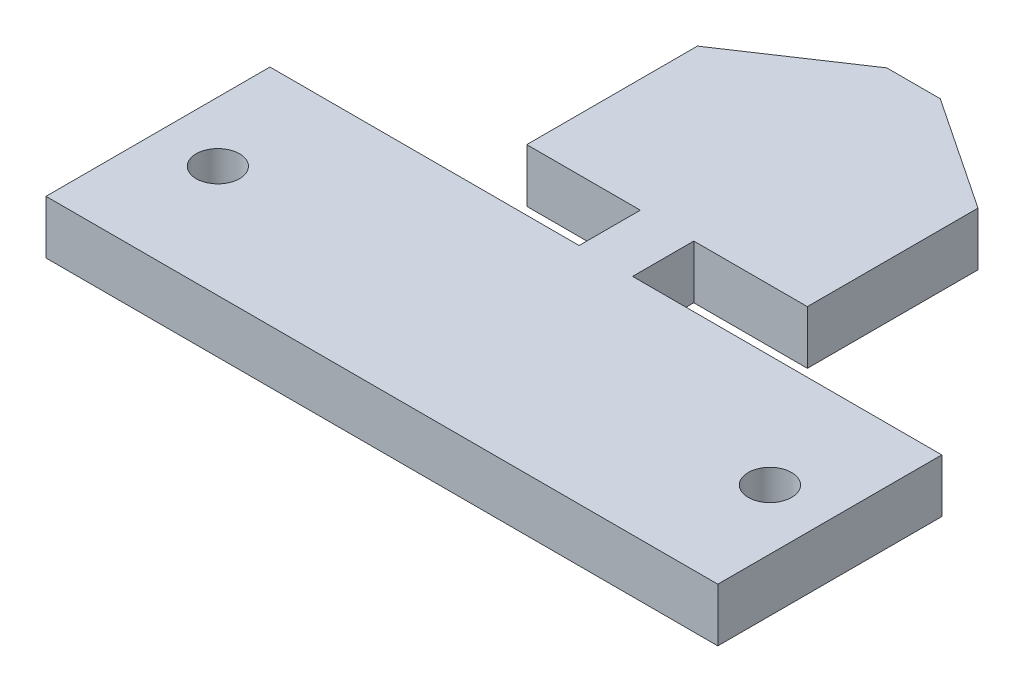
SolidWorks part; units mm, degrees
ref_plane "Front" through (0, 0, 0) normal (0, 0, 1) x (1, 0, 0)
ref_plane "Top" through (0, 0, 0) normal (0, 1, 0) x (1, 0, 0)
ref_plane "Right" through (0, 0, 0) normal (1, 0, 0) x (0, 0, -1)
sketch "Sketch1" plane through (0, 0, 0) normal (0, 1, 0) x (1, 0, 0)
  line L0 (-1.7907, 2.05) -> (-9.398, 2.05)
  line L2 (-1.7907, -2.05) -> (-1.7907, 2.05)
  line L4 (1.7907, -2.05) -> (1.7907, 2.05)
  line L7 (-9.398, 2.05) -> (-1.7907, 7.13)
  line L8 (-1.7907, 7.13) -> (1.7907, 7.13)
  line L9 (1.7907, 7.13) -> (9.398, 2.05)
  line L10 (9.398, 2.05) -> (1.7907, 2.05)
  line L11 (1.7907, -2.05) -> (22.5, -2.05)
  line L12 (-1.7907, -2.05) -> (-22.5, -2.05)
  line L13 (-22.5, -2.05) -> (-22.5, -17.05)
  line L14 (-22.5, -17.05) -> (22.5, -17.05)
  line L15 (22.5, -17.05) -> (22.5, -2.05)
  line L16 (22.5, -2.05) -> (1.7907, -2.05)
  point P0 (0, 0)
  point P17 (0, 7.13)
  point P19 (0, -17.05)
  point P24 (1.7907, 0)
  dimension "D1" = 18.796
  dimension "D2" = 3.5814
  dimension "D3" = 45
  dimension "D4" = 15
  dimension "D5" = 5.08
  dimension "D7" = 4.1
extrude "Boss-Extrude1" add sketch "Sketch1" along normal blind 3.5814 contours L14 L15 L11 L4 L10 L9 L8 L7 L0 L2 L12 L13
sketch "Sketch2" plane through (0, 3.5814, 0) normal (0, 1, 0) x (1, 0, 0)
  line L0 (0, 0) -> (0, -15.3387) construction
  line L2 (-22.5, -2.05) -> (-22.5, -17.05) construction
  circle A0 centre (-18.49, -9.55) radius 1.45
  circle A1 centre (18.49, -9.55) radius 1.45
  point P11 (-22.5, -9.55)
  dimension "D1" = 2.9
  dimension "D2" = 18.49
extrude "Cut-Extrude1" cut sketch "Sketch2" against normal through all
sketch "Sketch3" plane through (0, 3.5814, 0) normal (0, 1, 0) x (1, 0, 0)
  line L0 (-9.398, 2.05) -> (-9.398, 13.48)
  line L1 (-1.7907, 18.56) -> (1.7907, 18.56)
  line L2 (9.398, 13.48) -> (9.398, 2.05)
  line L4 (1.7907, 7.13) -> (9.398, 2.05) construction
  line L5 (-1.7907, 7.13) -> (1.7907, 7.13) construction
  line L6 (-9.398, 2.05) -> (-1.7907, 7.13) construction
  line L7 (1.7907, 7.13) -> (9.398, 2.05)
  line L8 (-1.7907, 7.13) -> (1.7907, 7.13)
  line L9 (-9.398, 2.05) -> (-1.7907, 7.13)
  line L10 (-9.398, 13.48) -> (-1.7907, 18.56)
  line L11 (-1.7907, 18.56) -> (1.7907, 18.56)
  line L12 (1.7907, 18.56) -> (9.398, 13.48)
  line L13 (0, 7.13) -> (0, 2.05) construction
  line L14 (0, 18.56) -> (0, 13.48) construction
  line L15 (0, 13.48) -> (9.398, 13.48) construction
  line L16 (9.398, 2.05) -> (1.7907, 2.05) construction
  point P13 (-3.8326, 19.83)
  point P15 (0, 0)
  point P16 (0, 14.3699)
  point P17 (0, 0)
  line M10 (9.398, 2.05) -> (1.7907, 7.13)
  line M11 (1.7907, 7.13) -> (-1.7907, 7.13)
  line M12 (-1.7907, 7.13) -> (-9.398, 2.05)
  dimension "D1" = 11.43
extrude "Boss-Extrude2" add sketch "Sketch3" against normal up to surface (3.5814 mm away) contours L12 L1 L10 L0 L2 M12 M11 M10 up to face at (-18.49, 0, 11)
